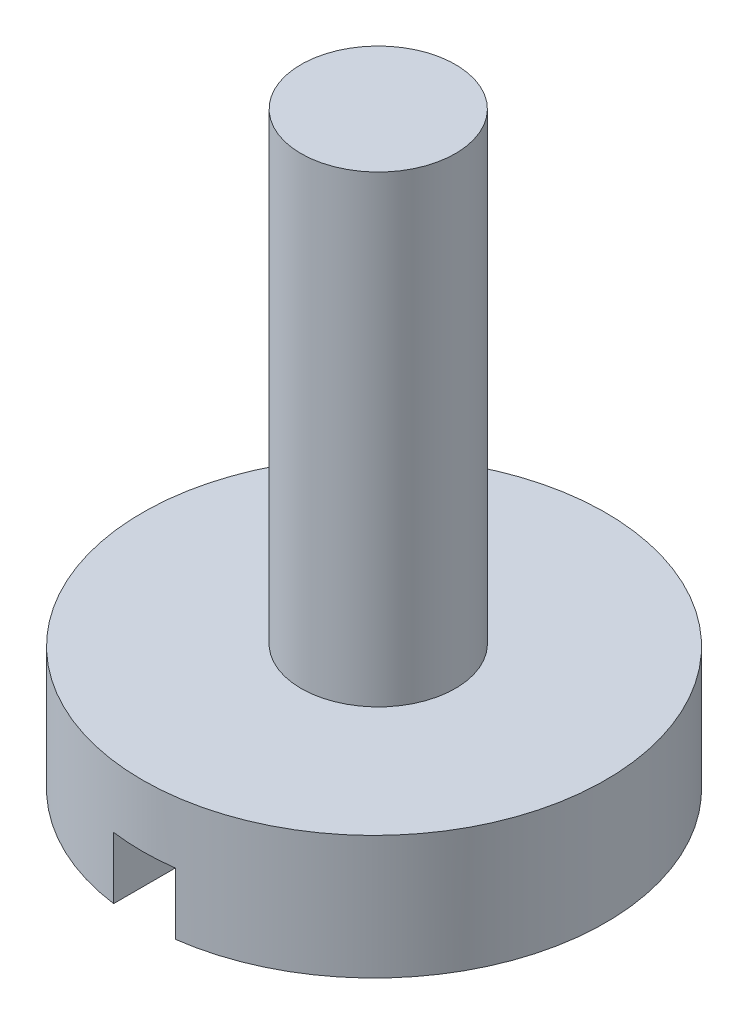
SolidWorks part; units mm, degrees
ref_plane "Спереди" through (0, 0, 0) normal (0, 0, 1) x (1, 0, 0)
ref_plane "Сверху" through (0, 0, 0) normal (0, 1, 0) x (1, 0, 0)
ref_plane "Справа" through (0, 0, 0) normal (1, 0, 0) x (0, 0, -1)
sketch "Эскиз1" plane through (0, 0, 0) normal (0, 1, 0) x (1, 0, 0)
  circle A0 centre (0, 0) radius 7.5
  dimension "D1" = 15
extrude "Бобышка-Вытянуть1" add sketch "Эскиз1" along normal blind 4
sketch "Эскиз2" plane through (0, 4, 0) normal (0, 1, 0) x (1, 0, 0)
  circle A0 centre (0, 0.1363) radius 2.5
  dimension "D1" = 5
extrude "Бобышка-Вытянуть2" add sketch "Эскиз2" along normal blind 15
sketch "Эскиз3" plane through (0, 0, 0) normal (0, -1, 0) x (1, 0, 0)
  line L1 (-1, 7.5) -> (1, 7.5)
  line L2 (-1, 7.5) -> (-1, -7.5)
  line L3 (-1, -7.5) -> (1, -7.5)
  line L4 (1, 7.5) -> (1, -7.5)
  line L5 (-1, 7.5) -> (1, -7.5) construction
  line L6 (-1, -7.5) -> (1, 7.5) construction
  circle A0 centre (0, 0) radius 7.5 construction
  point P0 (0, 0)
  dimension "D1" = 2
extrude "Вырез-Вытянуть1" cut sketch "Эскиз3" against normal blind 2
